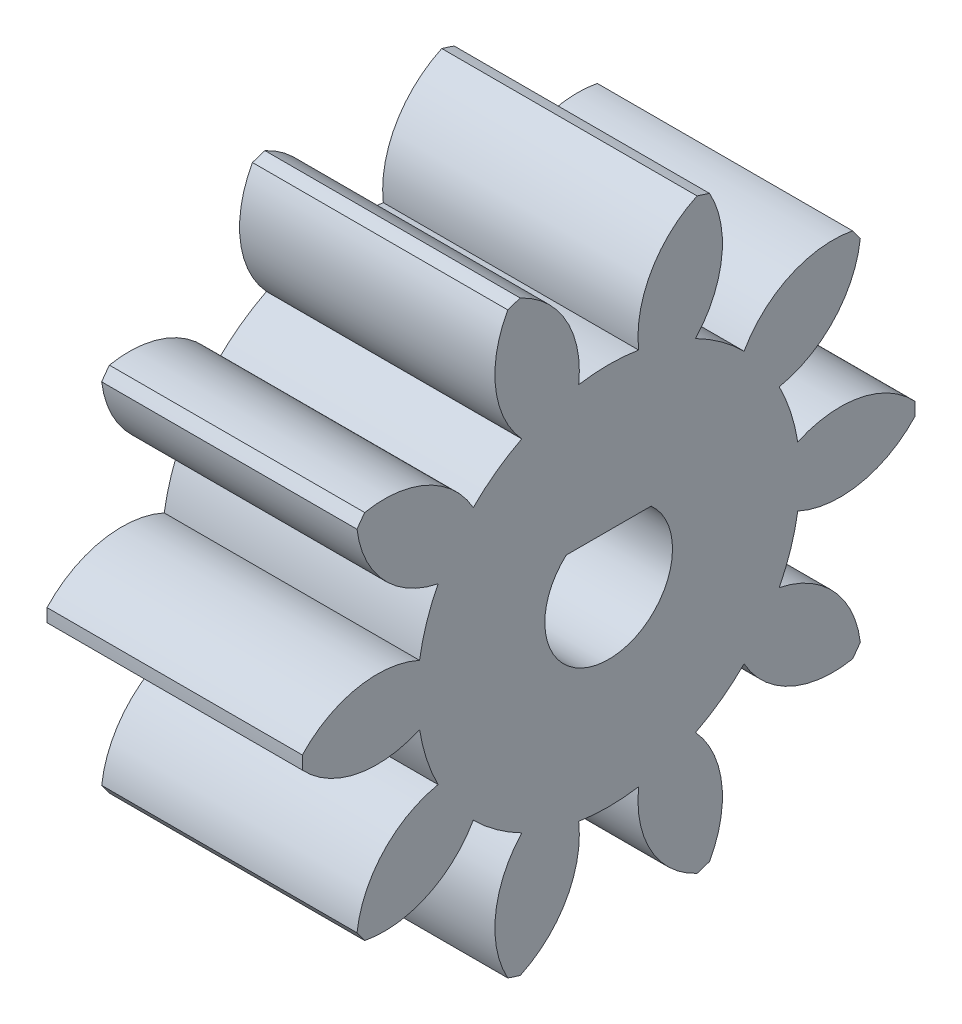
SolidWorks part; units mm, degrees
ref_plane "Plane1" through (0, 0, 0) normal (0, 0, 1) x (1, 0, 0)
ref_plane "Plane2" through (0, 0, 0) normal (0, 1, 0) x (1, 0, 0)
ref_plane "Plane3" through (0, 0, 0) normal (1, 0, 0) x (0, 0, -1)
sketch "HoldingSke" plane through (0, 0, 0) normal (0, 1, 0) x (1, 0, 0)
  line L0 (0, 0) -> (0.4924, -0.0868)
  line L1 (-15, 0) -> (100, 0) construction
  line L2 (0, 0) -> (-2.1039, 2.3779)
  line L3 (0, 0) -> (-11.863, 4.5341)
  line L4 (0, 0) -> (8.5048, 1.4996)
  line L5 (0, 0) -> (-46.8476, -17.4728)
  line L6 (0, 0) -> (-8.2896, -5.593)
  line L7 (-2.1039, 2.3779) -> (8.6586, 51.2059)
  line L8 (-76.2, 54.61) -> (-75.3, 54.61)
  line L9 (-71.009, 38.7566) -> (-53.1078, 45.2721)
  line L10 (-76.2, 71.12) -> (104.1128, 71.12)
  line L11 (0, 0) -> (-10, 0)
  line L12 (-76.2, 101.6) -> (-76.133, 101.6)
  line L13 (24.9733, 27.94) -> (52.9518, 28.4284)
  line L14 (24.9733, 27.94) -> (24.9743, 27.94)
  line L15 (24.9733, 27.94) -> (100.4006, 29.5858)
  line L16 (-63.627, -2) -> (-12.827, -2)
  circle A0 centre (0, 0) radius 2.5
  circle A1 centre (0, 0) radius 7.499
  circle A2 centre (0, 0) radius 37.5
  circle A3 centre (0, 0) radius 2.5
  dimension "MHD" = 14.998
  dimension "Hub_dia" = 75
  dimension "Bore" = 5
  dimension "MBD" = 5
  dimension "Num_teeth" = 10
  dimension "Pitch" = 0.5
  dimension "Overall_len" = 50
  dimension "Show_teeth" = 10
  dimension "Thickness" = 10
  dimension "OAL" = 50.0001
  dimension "T_dim" = 0.9
  dimension "Ap" = 20
  dimension "H" = 19.05
  dimension "Pitch_radius" = 180.3128
  dimension "Width" = 10
  dimension "Backlash" = 0.067
  dimension "Addendum_fac" = 1
  dimension "Dedendum_fac" = 1.25
  dimension "Clearance_fac" = 0.25
  dimension "Dedendum_add" = 0.001
  dimension "Module" = 2
sketch "BasProSke" plane through (0, 0, 0) normal (0, 1, 0) x (1, 0, 0)
  line L0 (-10, 0) -> (60, 0) construction
  line L1 (0, 0) -> (0, 12)
  line L2 (0, 0) -> (10, 0)
  line L3 (10, 0) -> (10, 12)
  line L4 (10, 12) -> (0, 12)
  dimension "Thickness" = 10
  dimension "Diameter" = 24
revolve "Base-Revolve" add sketch "BasProSke" angle 360 about L0
sketch "TooCutSke" plane through (0, 0, 0) normal (1, 0, 0) x (0, 0, -1)
  line L1 (0, 0) -> (0, 107) construction
  line L2 (0, 0) -> (-1.6814, 9.8576) construction
  line L3 (0, 0) -> (-6.1153, 18.8209) construction
  line L4 (-1.6814, 9.8576) -> (-3.0576, 9.4105) construction
  arc A0 (1.1737, 7.4066) -> (-1.1737, 7.4066) centre (0, 0) ccw
  arc A1 (3.4979, 11.5054) -> (-3.4979, 11.5054) centre (0, 0) ccw
  circle A2 centre (0, 0) radius 10 construction
  circle A3 centre (0, 0) radius 9.3969 construction
  arc A4 (-1.1737, 7.4066) -> (-3.4979, 11.5054) centre (-5.1477, 7.8615) ccw
  arc A5 (3.4979, 11.5054) -> (1.1737, 7.4066) centre (5.1477, 7.8615) ccw
  dimension "Root_dia" = 14.998
  dimension "Overcut_dia" = 24.0508
  dimension "Pitch_dia" = 20
  dimension "Base_dia" = 18.7939
  dimension "Flank_rad" = 4
  dimension "Half_ang" = 18
  dimension "Half_CT" = 1.4471
extrude "ToothCut" cut sketch "TooCutSke" along normal through all
fillet "Breaks" [suppressed] radius 0.04
fillet "RootFillets" [suppressed] radius 0.501
pattern_circular "TeethCuts" count 10 every 36 about axis through (-10, 0, 0) along (1, 0, 0) of "ToothCut", "RootFillets", "Breaks"
sketch "HubNeaOneSke" plane through (0, 0, 0) normal (-1, 0, 0) x (0, 0, 1)
  circle A0 centre (0, 0) radius 7.499
  dimension "Diameter" = 14.998
extrude "HubNearOne" [suppressed] add sketch "HubNeaOneSke" along normal blind 40.0001
sketch "HubNeaBotSke" plane through (0, 0, 0) normal (-1, 0, 0) x (0, 0, 1)
  circle A0 centre (0, 0) radius 7.499
  dimension "Diameter" = 14.998
extrude "HubNearBoth" [suppressed] add sketch "HubNeaBotSke" along normal blind 20
ref_plane "FarPln" through (10, 0, 0) normal (1, 0, 0) x (0, 0, -1)
sketch "HubFarSke" plane through (10, 0, 0) normal (1, 0, 0) x (0, 0, -1)
  circle A0 centre (0, 0) radius 7.499
  dimension "Diameter" = 14.998
extrude "HubFar" [suppressed] add sketch "HubFarSke" along normal blind 20
sketch "BorSke" plane through (0, 0, 0) normal (1, 0, 0) x (0, 0, -1)
  circle A0 centre (0, 0) radius 2.5
  dimension "Diameter" = 5
extrude "Bore" cut sketch "BorSke" along normal mid plane 100.0001
sketch "KeySke" plane through (0, 0, 0) normal (1, 0, 0) x (0, 0, -1)
  line L0 (-1, 0) -> (-1, 3.4)
  line L1 (-1, 3.4) -> (1, 3.4)
  line L2 (1, 3.4) -> (1, 0)
  line L3 (0, 0) -> (0, 34) construction
  line L4 (-1, 0) -> (1, 0)
  dimension "Offset" = 3.4
  dimension "Width" = 2
extrude "Keyway" [suppressed] cut sketch "KeySke" along normal mid plane 100.0001
pattern_circular "Keyway2" [suppressed] count 2 every 90 about axis through (-10, 0, 0) along (1, 0, 0)
sketch "Sketch1" plane through (10, 0, 0) normal (1, 0, 0) x (0, 0, -1)
  line L0 (-1.6606, 1.8688) -> (1.6606, 1.8688)
  line L1 (-2.0318, -2.5) -> (2.5035, -2.5) construction
  circle A0 centre (0, 0) radius 2.5 construction
  arc A1 (1.6606, 1.8688) -> (-1.6606, 1.8688) centre (0, 0) ccw
  dimension "D1" = 4.3688
extrude "Boss-Extrude1" add sketch "Sketch1" against normal up to surface (10 mm away) up to face at (0, 0, -2.5)
equation "' \"Module@HoldingSke\" = 6.35"
equation "' \"Num_teeth@HoldingSke\" = 12"
equation "' \"Ap@HoldingSke\" =  20"
equation "' \"Ap@HoldingSke\" = 20"
equation "' \"Width@HoldingSke\" = 0.5 * 25.4"
equation "' \"Hub_dia@HoldingSke\"= 1 * 25.4"
equation "' \"Hub_dia@HoldingSke\" = 1 * 25.4"
equation "' \"Overall_len@HoldingSke\" = 1.0 * 25.4"
equation "' \"Bore@HoldingSke\" = 0.75 * 25.4"
equation "' \"T_dim@HoldingSke\" = 0.1 * 25.4"
equation "' \"Width@KeySke\" = 0.25 * 25.4"
equation "' \"Show_teeth@HoldingSke\" = 13"
equation "' \"Backlash@HoldingSke\" = 0.009 * 25.4"
equation "' \"Addendum_fac@HoldingSke\" = 1.0"
equation "' \"Dedendum_fac@HoldingSke\" = 1.25"
equation "' \"Dedendum_add@HoldingSke\" = 0.00005 * 25.4"
equation "' \"Clearance_fac@HoldingSke\" = 0.25"
equation "\"Pitch@HoldingSke\" = 1 / \"Module@HoldingSke\""
equation "\"Overcut_dia@TooCutSke\" = (\"Num_teeth@HoldingSke\" + 2 * \"Addendum_fac@HoldingSke\") / \"Pitch@HoldingSke\" + 0.002 * 25.4"
equation "\"Pitch_dia@TooCutSke\" = \"Num_teeth@HoldingSke\" / \"Pitch@HoldingSke\""
equation "\"Base_dia@TooCutSke\" = \"Num_teeth@HoldingSke\" / \"Pitch@HoldingSke\" * cos((\"Ap@HoldingSke\"  * 3.14159265 / 180))"
equation "\"Root_dia@TooCutSke\" = (\"Num_teeth@HoldingSke\" + 2) / \"Pitch@HoldingSke\" - 2 * (\"Addendum_fac@HoldingSke\" + \"Dedendum_fac@HoldingSke\") / \"Pitch@HoldingSke\" - \"Dedendum_add@HoldingSke\" * 2"
equation "\"Half_ang@TooCutSke\" = 180 / \"Num_teeth@HoldingSke\""
equation "\"Half_CT@TooCutSke\" = \"Num_teeth@HoldingSke\" / \"Pitch@HoldingSke\" * sin((3.14159265 / 2 / \"Num_teeth@HoldingSke\")) / 2 - 7 * \"Backlash@HoldingSke\" / 4"
equation "\"Flank_rad@TooCutSke\" = \"Num_teeth@HoldingSke\" / \"Pitch@HoldingSke\" / 5"
equation "\"Radius@RootFillets\" = \"Clearance_fac@HoldingSke\" / \"Pitch@HoldingSke\" + \"Dedendum_add@HoldingSke\""
equation "\"Break_rad@Breaks\" = 0.02 / \"Pitch@HoldingSke\""
equation "\"Thickness@HoldingSke\" = \"Width@HoldingSke\""
equation "\"OAL@HoldingSke\" = \"Thickness@HoldingSke\""
equation "\"MHD@HoldingSke\" = (\"Num_teeth@HoldingSke\" + 2) / \"Pitch@HoldingSke\" - 2 * (\"Addendum_fac@HoldingSke\" + \"Dedendum_fac@HoldingSke\")  / \"Pitch@HoldingSke\" - \"Dedendum_add@HoldingSke\" * 2"
equation "\"MBD@HoldingSke\" = (\"Num_teeth@HoldingSke\" + 2) / \"Pitch@HoldingSke\" - 2 * (\"Addendum_fac@HoldingSke\" + \"Dedendum_fac@HoldingSke\")  / \"Pitch@HoldingSke\" - \"Dedendum_add@HoldingSke\" * 2 - 0.002 * 25.4"
equation "\"MHD@HoldingSke\" = ((sgn( \"MHD@HoldingSke\" - \"Hub_dia@HoldingSke\" )-1)*( \"MHD@HoldingSke\" - \"Hub_dia@HoldingSke\" ))/-2+ \"Hub_dia@HoldingSke\""
equation "\"MBD@HoldingSke\" = ((sgn( \"MBD@HoldingSke\" - \"Bore@HoldingSke\" )-1)*( \"MBD@HoldingSke\" - \"Bore@HoldingSke\" ))/-2+ \"Bore@HoldingSke\""
equation "\"OAL@HoldingSke\" = ((sgn( \"OAL@HoldingSke\" - \"Overall_len@HoldingSke\" )+1)*( \"OAL@HoldingSke\" - \"Overall_len@HoldingSke\" ))/2 + \"Overall_len@HoldingSke\" + 0.000002 * 25.4"
equation "\"Num_teeth@TeethCuts\" = int( \"Show_teeth@HoldingSke\" ) + 1"
equation "\"Num_teeth@TeethCuts\" = ((sgn( \"Num_teeth@TeethCuts\" - \"Num_teeth@HoldingSke\" )-1)*( \"Num_teeth@TeethCuts\" - \"Num_teeth@HoldingSke\" ))/-2+ \"Num_teeth@HoldingSke\""
equation "\"Num_teeth@TeethCuts\" = ((sgn( \"Num_teeth@TeethCuts\" - 2.0)+1)*( \"Num_teeth@TeethCuts\" - 2.0))/2 +2.0"
equation "\"Angle@TeethCuts\" = 360.0 / \"Num_teeth@HoldingSke\""
equation "\"Diameter@BasProSke\" = (\"Num_teeth@HoldingSke\" + 2 * \"Addendum_fac@HoldingSke\") / \"Pitch@HoldingSke\""
equation "\"Thickness@BasProSke\"  = \"Thickness@HoldingSke\""
equation "' \"Fillet_rad@BasProSke\" =  \"Thickness@HoldingSke\" * 0.05"
equation "' \"Fillet_rad@BasProSke\" = \"Thickness@HoldingSke\" * 0.05"
equation "\"MHD@HoldingSke\" = ((sgn( \"MHD@HoldingSke\" - \"Root_dia@TooCutSke\" )-1)*( \"MHD@HoldingSke\" - \"Root_dia@TooCutSke\" ))/-2+ \"Root_dia@TooCutSke\""
equation "\"Diameter@HubNeaOneSke\" = \"MHD@HoldingSke\""
equation "\"Length@HubNearOne\" = \"OAL@HoldingSke\" - \"Thickness@BasProSke\""
equation "\"Diameter@HubNeaBotSke\" = \"MHD@HoldingSke\""
equation "\"Length@HubNearBoth\" = ( \"OAL@HoldingSke\" - \"Thickness@BasProSke\" ) / 2.0"
equation "\"Thickness@FarPln\" = \"Thickness@BasProSke\""
equation "\"Diameter@HubFarSke\" = \"MHD@HoldingSke\""
equation "\"Length@HubFar\" = ( \"OAL@HoldingSke\" - \"Thickness@BasProSke\" ) / 2.0"
equation "\"Diameter@BorSke\" = \"MBD@HoldingSke\""
equation "\"D1@Bore\" = \"OAL@HoldingSke\" * 2.0"
equation "\"D1@Keyway\" = \"OAL@HoldingSke\" * 2.0"
equation "\"Offset@KeySke\" = \"T_dim@HoldingSke\" + \"MBD@HoldingSke\" / 2.0"
